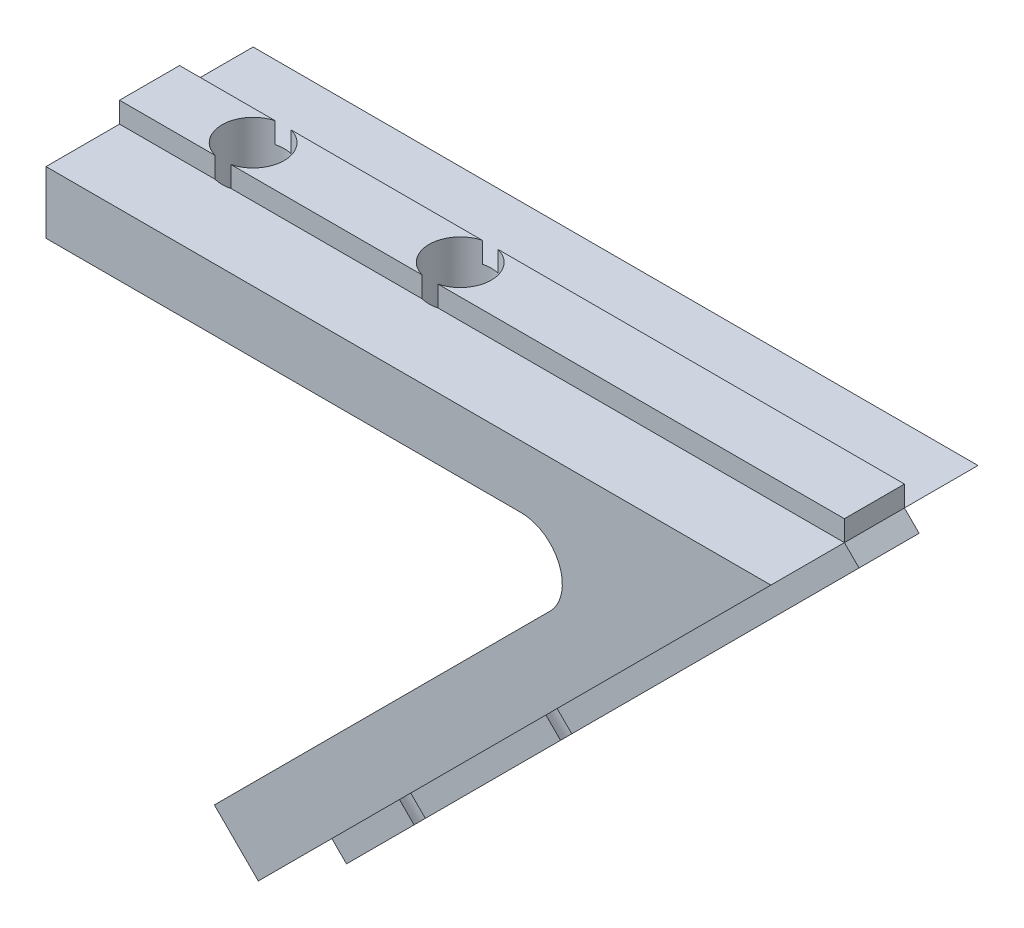
SolidWorks part; units mm, degrees
ref_plane "Front Plane" through (0, 0, 0) normal (0, 0, 1) x (1, 0, 0)
ref_plane "Top Plane" through (0, 0, 0) normal (0, 1, 0) x (1, 0, 0)
ref_plane "Right Plane" through (0, 0, 0) normal (1, 0, 0) x (0, 0, -1)
sketch "Esquisse1" plane through (0, 0, 0) normal (0, 0, 1) x (1, 0, 0)
  line L0 (0, 0) -> (35, 0)
  line L1 (35, 0) -> (10.2513, -24.7487)
  line L2 (10.2513, -24.7487) -> (8.1299, -22.6274)
  line L3 (8.1299, -22.6274) -> (24.3431, -6.4142)
  line L4 (0, 0) -> (0, -3)
  line L5 (0, -3) -> (22.9289, -3)
  arc A0 (24.3431, -6.4142) -> (22.9289, -3) centre (22.9289, -5) ccw
  dimension "D3" = 2
  dimension "D1" = 45
  dimension "D2" = 3
  dimension "D4" = 35
extrude "Boss.-Extru.1" add sketch "Esquisse1" along normal blind 10
sketch "Esquisse2" plane through (0, 0, 0) normal (0, 1, 0) x (1, 0, 0)
  line L0 (0, -10) -> (0, 0) construction
  line L1 (0, -6.45) -> (35, -6.45)
  line L2 (0, -6.45) -> (0, -3.55)
  line L3 (0, -3.55) -> (35, -3.55)
  line L4 (35, -6.45) -> (35, -3.55)
  line L5 (35, -10) -> (35, 0) construction
  point P8 (35, -5)
  point P9 (35, -5)
  dimension "D1" = 2.9
extrude "Boss.-Extru.2" add sketch "Esquisse2" along normal blind 1
sketch "Esquisse3" plane through (17.5, -17.5, 0) normal (0.7071, -0.7071, 0) x (0.7071, 0.7071, 0)
  line L1 (-10.2513, 3.55) -> (24.7487, 3.55)
  line L2 (-10.2513, 3.55) -> (-10.2513, 6.45)
  line L3 (-10.2513, 6.45) -> (24.7487, 6.45)
  line L4 (24.7487, 3.55) -> (24.7487, 6.45)
  line L5 (-10.2513, 10) -> (-10.2513, 0) construction
  line L6 (24.7487, 6.45) -> (24.7487, 3.55) construction
  point P4 (-10.2513, 5)
  point P5 (-10.2513, 5)
extrude "Boss.-Extru.3" add sketch "Esquisse3" along normal blind 1
sketch "Esquisse4" plane through (0, -3, 0) normal (0, -1, 0) x (1, 0, 0)
  line L0 (0, 10) -> (0, 0) construction
  circle A0 centre (5, 5) radius 1.5
  circle A1 centre (15, 5) radius 1.5
  point P8 (0, 5)
  dimension "D1" = 3
  dimension "D2" = 5
  dimension "D3" = 10
extrude "Enlèv. mat.-Extru.1" cut sketch "Esquisse4" against normal through all
sketch "Esquisse5" plane through (15.3787, -15.3787, 0) normal (-0.7071, 0.7071, 0) x (0.7071, 0.7071, 0)
  line L0 (-10.2513, -10) -> (-10.2513, 0) construction
  circle A0 centre (-5.2513, -5) radius 1.5
  circle A1 centre (4.7487, -5) radius 1.5
  point P7 (-10.2513, -5)
  dimension "D1" = 3
  dimension "D2" = 5
  dimension "D3" = 10
extrude "Enlèv. mat.-Extru.2" cut sketch "Esquisse5" against normal through all
